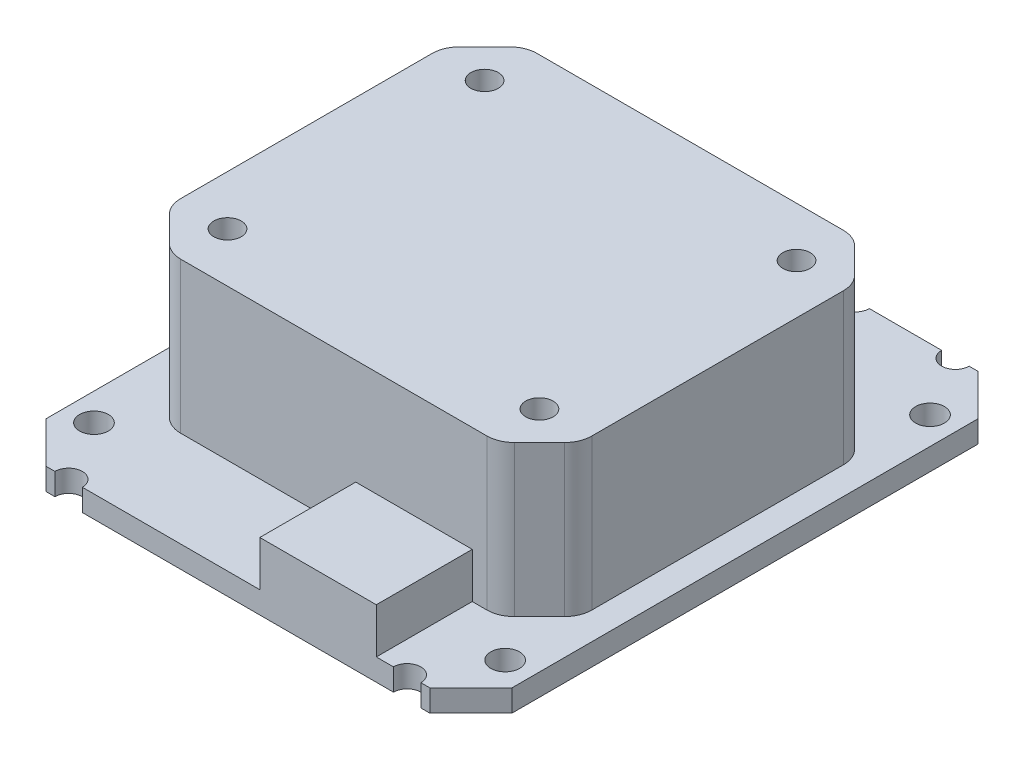
SolidWorks part; units mm, degrees
ref_plane "Front Plane" through (0, 0, 0) normal (0, 0, 1) x (1, 0, 0)
ref_plane "Top Plane" through (0, 0, 0) normal (0, 1, 0) x (1, 0, 0)
ref_plane "Right Plane" through (0, 0, 0) normal (1, 0, 0) x (0, 0, -1)
sketch "Sketch1" plane through (0, 0, 0) normal (0, 1, 0) x (1, 0, 0)
  line L0 (-17, 20) -> (17, -20)
  line L1 (-17, 20) -> (17, 20)
  line L2 (-17, 20) -> (-17, -20)
  line L3 (-17, -20) -> (17, -20)
  line L4 (17, 20) -> (17, -20)
  dimension "D1" = 34
  dimension "D2" = 40
extrude "Boss-Extrude1" add sketch "Sketch1" along normal blind 1.6 contours L2 L3 L0 | L4 L1 L0
chamfer "Chamfer1" distance 3 angle 45 4 edges at (-17, 0.8, 20) (17, 0.8, 20) (17, 0.8, -20) (-17, 0.8, -20)
sketch "Sketch2" plane through (0, 1.6, 0) normal (0, 1, 0) x (1, 0, 0)
  line L1 (-15, 13) -> (15, 13)
  line L2 (-15, 13) -> (-15, -13)
  line L3 (-15, -13) -> (15, -13)
  line L4 (15, 13) -> (15, -13)
  line L5 (-15, 13) -> (15, -13)
  point P11 (0, 13)
  dimension "D2" = 30
  dimension "D3" = 26
extrude "Boss-Extrude2" add sketch "Sketch2" along normal blind 11 contours L1 L5 L4 | L5 L2 L3
chamfer "Chamfer2" distance 3 angle 45 4 edges at (-15, 7.1, -13) (15, 7.1, -13) (15, 7.1, 13) (-15, 7.1, 13)
fillet "Fillet1" radius 2 8 edges at (-15, 7.1, 10) (-12, 7.1, 13) (12, 7.1, 13) (15, 7.1, 10) (15, 7.1, -10) (12, 7.1, -13) (-15, 7.1, -10) (-12, 7.1, -13)
sketch "Sketch3" plane through (0, 12.6, 0) normal (0, 1, 0) x (1, 0, 0)
  line L0 (-12.5858, 12.4142) -> (-14.4142, 10.5858) construction
  circle A0 centre (-11.3787, 9.3787) radius 1
  dimension "D1" = 2
  dimension "D2" = 3
extrude "Cut-Extrude1" cut sketch "Sketch3" against normal up to surface (11 mm away) up to face at (0, 1.6, 0)
sketch "Sketch4" plane through (0, 12.6, 0) normal (0, 1, 0) x (1, 0, 0)
  line L0 (15, -15.5) -> (-15, 15.5) construction
  line L1 (-15, 15.5) -> (15, 15.5) construction
  line L2 (-15, 15.5) -> (-15, -15.5) construction
  line L3 (-15, -15.5) -> (15, -15.5) construction
  line L4 (15, 15.5) -> (15, -15.5) construction
  circle A0 centre (15, 15.5) radius 1.05
  dimension "D3" = 2.1
  dimension "D1" = 30
  dimension "D2" = 31
extrude "Cut-Extrude2" cut sketch "Sketch4" against normal through all
sketch "Sketch5" plane through (0, 1.6, 0) normal (0, 1, 0) x (1, 0, 0)
  line L0 (-14, 20) -> (14, 20) construction
  line L1 (-12.35, 20) -> (12.35, 20) construction
  circle A0 centre (-12.35, 20) radius 1
  point P5 (0, 20)
  dimension "D2" = 2
  dimension "D1" = 24.7
extrude "Cut-Extrude3" cut sketch "Sketch5" against normal through all
mirror "Mirror1" about plane through (0, 0, 0) normal (0, 0, 1) of "Cut-Extrude3", "Cut-Extrude1", "Cut-Extrude2" second plane through (0, 0, 0) second plane normal (1, 0, 0)
sketch "Sketch6" plane through (0, 1.6, 0) normal (0, 1, 0) x (1, 0, 0)
  line L0 (-11.1716, -13) -> (11.1716, -13) construction
  line L1 (1.6, -13) -> (10.1, -13)
  line L2 (1.6, -13) -> (1.6, -20)
  line L3 (1.6, -20) -> (10.1, -20)
  line L4 (10.1, -13) -> (10.1, -20)
  line L5 (-11.35, -20) -> (11.35, -20) construction
  arc A0 (13.35, -20) -> (11.35, -20) centre (12.35, -20) ccw construction
  dimension "D1" = 8.5
  dimension "D2" = 2.25
extrude "Boss-Extrude3" add sketch "Sketch6" along normal blind 3.3
sketch "Sketch7" plane through (0, 1.6, 0) normal (0, 1, 0) x (1, 0, 0)
  line L0 (-11.35, 20) -> (11.35, 20) construction
  circle A0 centre (0, 18) radius 0.5
  circle A1 centre (0, 20) radius 1
  point P6 (0, 0)
  dimension "D2" = 2
  dimension "D3" = 1
  dimension "D1" = 2
extrude "Cut-Extrude4" cut sketch "Sketch7" against normal through all
pattern_linear "LPattern1" count 3 spacing 2.54 along (1, 0, 0) count 3 spacing 2.54 along (-1, 0, 0) of "Cut-Extrude4"
